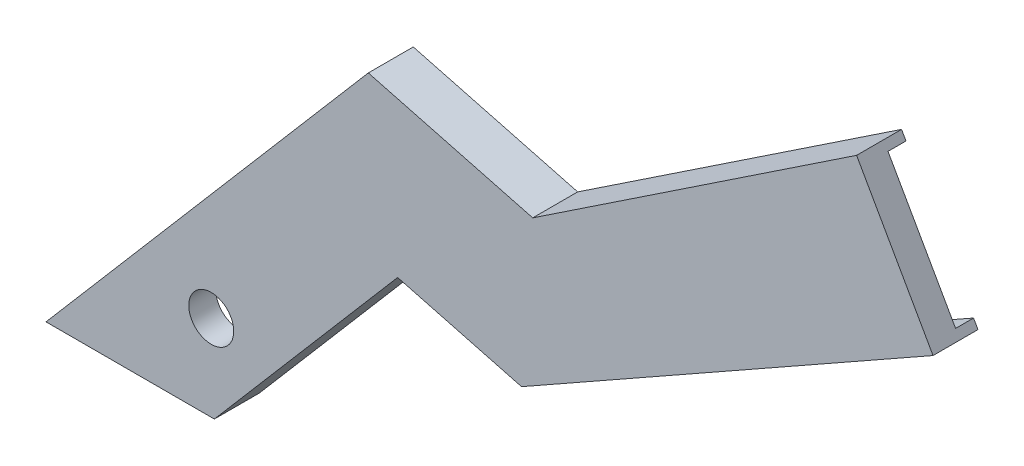
SolidWorks part; units mm, degrees
ref_plane "Front" through (0, 0, 0) normal (0, 0, 1) x (1, 0, 0)
ref_plane "Top" through (0, 0, 0) normal (0, 1, 0) x (1, 0, 0)
ref_plane "Right" through (0, 0, 0) normal (1, 0, 0) x (0, 0, -1)
sketch "Sketch1" plane through (0, 0, 0) normal (0, 0, 1) x (1, 0, 0)
  line L0 (72.0271, 48.0553) -> (89.0276, 17.9923)
  line L1 (57.8758, 38.6138) -> (114.7319, 76.5473) construction
  line L2 (196.4536, 80.4206) -> (72.5608, 8.423) construction
  line L3 (89.0276, 17.9923) -> (-2.4875, -33.7591)
  line L4 (-2.4875, -33.7591) -> (-30.0371, -26.4994)
  line L5 (-30.0371, -26.4994) -> (-70.8031, -74.1528)
  line L6 (-70.8031, -74.1528) -> (-108.2425, -74.1528)
  line L7 (-108.2425, -74.1528) -> (-36.5644, 9.6352)
  line L10 (-36.5644, 9.6352) -> (0, 0)
  line L11 (0, 0) -> (72.0271, 48.0553)
  circle A0 centre (-71.4908, -55.1047) radius 5
  dimension "D1" = 10
extrude "Boss-Extrude1" add sketch "Sketch1" against normal blind 10
sketch "Sketch2" plane through (0, 0, -10) normal (0, 0, -1) x (-1, 0, 0)
  line L8 (-71.3461, 45.1967) -> (-73.0143, 46.3097)
  line L9 (-89.0276, 17.9923) -> (-72.0271, 48.0553) construction
  line L10 (-86.3022, 18.7488) -> (-88.0432, 19.7333)
  line L11 (-88.0432, 19.7333) -> (-73.0143, 46.3097)
  line L12 (103.8996, -72.1528) -> (105.6105, -74.1528)
  line L13 (108.2425, -74.1528) -> (70.8031, -74.1528) construction
  line L14 (71.7241, -72.1528) -> (73.4351, -74.1528)
  line L15 (73.4351, -74.1528) -> (105.6105, -74.1528)
  line L16 (-0.361, -2.1634) -> (-71.3461, 45.1967)
  line L17 (-71.3461, 45.1967) -> (-86.3022, 18.7488)
  line L18 (-86.3022, 18.7488) -> (2.7641, -31.6179)
  line L19 (2.7641, -31.6179) -> (30.741, -24.2456)
  line L20 (30.741, -24.2456) -> (71.7241, -72.1528)
  line L21 (71.7241, -72.1528) -> (103.8996, -72.1528)
  line L22 (103.8996, -72.1528) -> (35.8605, 7.3814)
  line L23 (35.8605, 7.3814) -> (-0.361, -2.1634)
  line L24 (-0.361, -2.1634) -> (-71.3461, 45.1967)
  line L26 (-86.3022, 18.7488) -> (2.7641, -31.6179)
  line L27 (2.7641, -31.6179) -> (30.741, -24.2456)
  line L28 (30.741, -24.2456) -> (71.7241, -72.1528)
  line L30 (103.8996, -72.1528) -> (35.8605, 7.3814)
  line L31 (35.8605, 7.3814) -> (-0.361, -2.1634)
  dimension "D1" = 2
extrude "Cut-Extrude1" cut sketch "Sketch2" against normal blind 4
